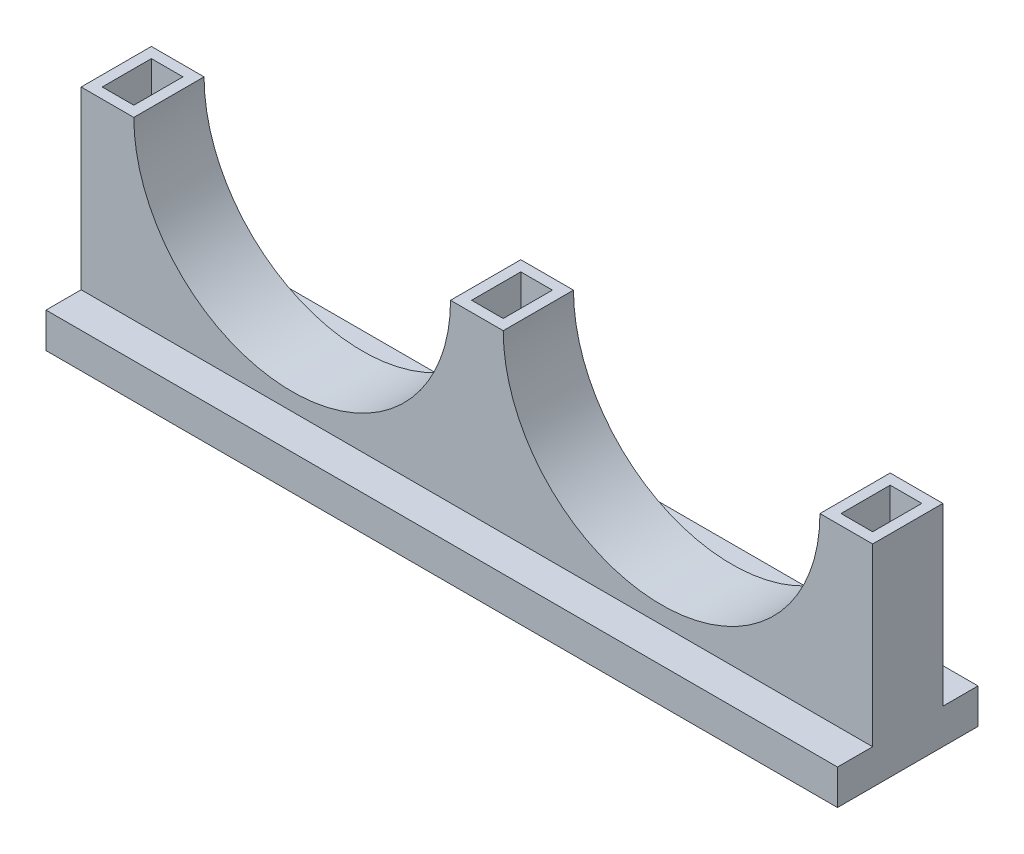
SolidWorks part; units mm, degrees
ref_plane "Front Plane" through (0, 0, 0) normal (0, 0, 1) x (1, 0, 0)
ref_plane "Top Plane" through (0, 0, 0) normal (0, 1, 0) x (1, 0, 0)
ref_plane "Right Plane" through (0, 0, 0) normal (1, 0, 0) x (0, 0, -1)
sketch "Sketch7" plane through (0, 0, 0) normal (0, 0, 1) x (1, 0, 0)
  line L0 (0, 10) -> (0, 60)
  line L1 (105.17, 60) -> (120.17, 60)
  line L2 (105.17, 60) -> (15, 60) construction
  line L3 (0, 60) -> (15, 60)
  line L4 (210.34, 60) -> (120.17, 60) construction
  line L5 (210.34, 60) -> (225.34, 60)
  line L6 (225.34, 60) -> (225.34, 0)
  line L7 (0, 10) -> (0, 0)
  line L8 (0, 0) -> (225.34, 0)
  arc A0 (15, 60) -> (105.17, 60) centre (60.085, 60) ccw
  arc A1 (120.17, 60) -> (210.34, 60) centre (165.255, 60) ccw
  dimension "D1" = 90.17
  dimension "D2" = 10
  dimension "5" = 15
  dimension "D3" = 50
extrude "Boss-Extrude2" add sketch "Sketch7" along normal blind 20
sketch "Sketch8" plane through (0, 60, 0) normal (0, 1, 0) x (1, 0, 0)
  line L8 (12, -3) -> (3, -3)
  line L9 (3, -3) -> (3, -17)
  line L10 (3, -17) -> (12, -17)
  line L11 (12, -17) -> (12, -3)
  line L12 (12, -3) -> (3, -3)
  line L13 (3, -3) -> (3, -17)
  line L14 (3, -17) -> (12, -17)
  line L15 (12, -17) -> (12, -3)
  line L21 (213.34, -17) -> (222.34, -17)
  line L22 (222.34, -17) -> (222.34, -3)
  line L23 (213.34, -3) -> (213.34, -17)
  line L24 (222.34, -3) -> (213.34, -3)
  line L25 (213.34, -17) -> (222.34, -17)
  line L26 (222.34, -17) -> (222.34, -3)
  line L27 (213.34, -3) -> (213.34, -17)
  line L28 (222.34, -3) -> (213.34, -3)
  line L43 (108.17, -17) -> (117.17, -17)
  line L44 (108.17, -3) -> (108.17, -17)
  line L45 (117.17, -17) -> (117.17, -3)
  line L46 (117.17, -3) -> (108.17, -3)
  line L47 (108.17, -17) -> (117.17, -17)
  line L48 (108.17, -3) -> (108.17, -17)
  line L49 (117.17, -17) -> (117.17, -3)
  line L50 (117.17, -3) -> (108.17, -3)
  dimension "D1" = 3
  dimension "D2" = 3
  dimension "D3" = 3
extrude "Cut-Extrude1" cut sketch "Sketch8" against normal blind 10 draft 1
sketch "Sketch9" plane through (0, 0, 20) normal (0, 0, 1) x (1, 0, 0)
  line L0 (0, 60) -> (0, 0) construction
  line L1 (225.34, 0) -> (0, 0)
  line L2 (225.34, 0) -> (225.34, 10)
  line L3 (225.34, 10) -> (0, 10)
  line L4 (0, 0) -> (0, 10)
  dimension "D1" = 10
extrude "Boss-Extrude3" add sketch "Sketch9" along normal blind 20 and the other way blind 20 from offset 10
